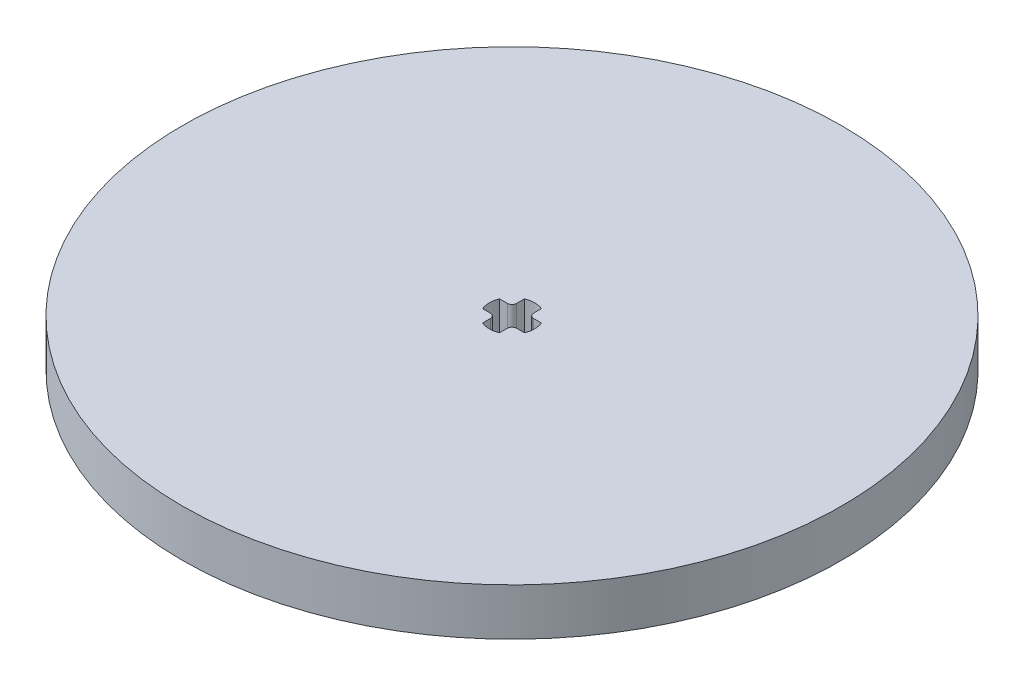
SolidWorks part; units mm, degrees
ref_plane "Front Plane" through (0, 0, 0) normal (0, 0, 1) x (1, 0, 0)
ref_plane "Top Plane" through (0, 0, 0) normal (0, 1, 0) x (1, 0, 0)
ref_plane "Right Plane" through (0, 0, 0) normal (1, 0, 0) x (0, 0, -1)
sketch "Sketch1" plane through (0, 0, 0) normal (0, 1, 0) x (1, 0, 0)
  line L1 (-78.3991, 0) -> (78.3991, 0) construction
  line L4 (-18.8444, 18.8444) -> (18.8444, -18.8444) construction
  line L5 (-23.8815, -23.8815) -> (23.8815, 23.8815) construction
  circle A0 centre (0, 0) radius 35
  line B0 (-2.2249, 0.9) -> (-2.2249, -0.9) construction
  line B1 (0.9, 2.2249) -> (-0.9, 2.2249) construction
  line B2 (2.2249, 0.9) -> (2.2249, -0.9) construction
  line B3 (0.9, -2.2249) -> (-0.9, -2.2249) construction
  line B4 (-1.4, 0.9) -> (-2.2249, 0.9)
  line B5 (0.9, -2.2249) -> (0.9, -1.4)
  line B6 (-0.9, -2.2249) -> (-0.9, -1.4)
  line B7 (0.9, -2.2249) -> (-0.9, 2.2249) construction
  line B8 (0.9, 2.2249) -> (-0.9, -2.2249) construction
  line B9 (2.2249, 0.9) -> (1.4, 0.9)
  line B10 (2.2249, -0.9) -> (1.4, -0.9)
  line B11 (2.2249, 0.9) -> (-2.2249, -0.9) construction
  line B12 (2.2249, -0.9) -> (-2.2249, 0.9) construction
  line B13 (-0.9, 1.4) -> (-0.9, 2.2249)
  line B14 (0.9, 1.4) -> (0.9, 2.2249)
  line B15 (-1.4, -0.9) -> (-2.2249, -0.9)
  arc B16 (-2.2249, 0.9) -> (-2.2249, -0.9) centre (0, 0) ccw
  arc B17 (-1.4, -0.9) -> (-0.9, -1.4) centre (-1.4, -1.4) cw
  arc B18 (0.9, -1.4) -> (1.4, -0.9) centre (1.4, -1.4) cw
  arc B19 (1.4, 0.9) -> (0.9, 1.4) centre (1.4, 1.4) cw
  arc B20 (-0.9, 1.4) -> (-1.4, 0.9) centre (-1.4, 1.4) cw
  arc B21 (0.9, 2.2249) -> (-0.9, 2.2249) centre (0, 0) ccw
  arc B22 (2.2249, -0.9) -> (2.2249, 0.9) centre (0, 0) ccw
  arc B23 (-0.9, -2.2249) -> (0.9, -2.2249) centre (0, 0) ccw
  dimension "D1" = 70
sketch_block_instance "Axle Section Block-1"
sketch_block "Axle Section Block" parameters "D1"=4.8, "D3"=0.5, "D2"=1.8
extrude "Boss-Extrude1" add sketch "Sketch1" along normal blind 5
